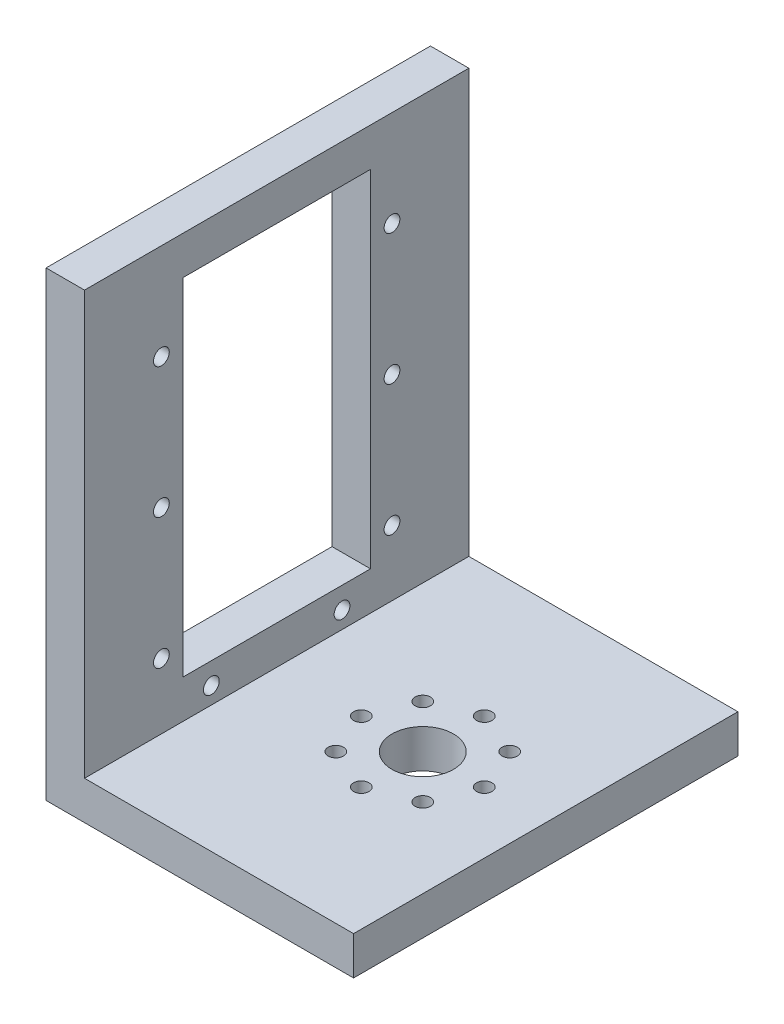
SolidWorks part; units mm, degrees
material "ABS"
ref_plane "Front Plane" through (0, 0, 0) normal (0, 0, 1) x (1, 0, 0)
ref_plane "Top Plane" through (0, 0, 0) normal (0, 1, 0) x (1, 0, 0)
ref_plane "Right Plane" through (0, 0, 0) normal (1, 0, 0) x (0, 0, -1)
sketch "Sketch1" plane through (0, 0, 0) normal (0, 1, 0) x (1, 0, 0)
  line L0 (40, 25) -> (24, 25) construction
  line L1 (0, 0) -> (40, 0)
  line L2 (0, 0) -> (0, 50)
  line L3 (0, 50) -> (40, 50)
  line L4 (40, 0) -> (40, 50)
  line L5 (24, 33) -> (24, 25) construction
  circle A0 centre (24, 25) radius 4
  circle A1 centre (24, 33) radius 1
  circle A2 centre (29.6569, 30.6569) radius 1
  circle A3 centre (32, 25) radius 1
  circle A4 centre (29.6569, 19.3431) radius 1
  circle A5 centre (24, 17) radius 1
  circle A6 centre (18.3431, 19.3431) radius 1
  circle A7 centre (16, 25) radius 1
  circle A8 centre (18.3431, 30.6569) radius 1
  point P26 (24, 25)
  dimension "D3" = 8
  dimension "D5" = 2
  dimension "D1" = 40
  dimension "D2" = 50
  dimension "D4" = 16
  dimension "D7" = 8
  dimension "D6" = 8
extrude "Boss-Extrude1" add sketch "Sketch1" along normal blind 5
sketch "Sketch3" plane through (0, 0, 0) normal (0, 1, 0) x (1, 0, 0)
  line L0 (40, 50) -> (0, 50) construction
  line L1 (0, 0) -> (5, 0)
  line L2 (0, 0) -> (0, 50)
  line L3 (0, 50) -> (5, 50)
  line L4 (5, 0) -> (5, 50)
  dimension "D1" = 5
extrude "Boss-Extrude2" add sketch "Sketch3" along normal blind 60
sketch "Sketch4" plane through (0, 0, 0) normal (-1, 0, 0) x (0, 0, 1)
  line L0 (-25, 60) -> (-25, 23.7384) construction
  line L1 (-50, 60) -> (0, 60) construction
  line L2 (-40, 47.5) -> (-10, 47.5) construction
  line L3 (-37.2, 10) -> (-12.8, 10)
  line L4 (-37.2, 10) -> (-37.2, 55)
  line L5 (-37.2, 55) -> (-12.8, 55)
  line L6 (-12.8, 10) -> (-12.8, 55)
  line L7 (-40, 30.5) -> (-10, 30.5) construction
  line L8 (-40, 13.5) -> (-33.5, 7.2) construction
  line L9 (-40, 30.5) -> (-40, 13.5) construction
  circle A0 centre (-40, 47.5) radius 1.025
  circle A1 centre (-10, 47.5) radius 1.025
  circle A2 centre (-40, 30.5) radius 1.025
  circle A5 centre (-10, 30.5) radius 1.025
  circle A8 centre (-40, 13.5) radius 1.025
  circle A9 centre (-33.5, 7.2) radius 1.025
  circle A10 centre (-16.5, 7.2) radius 1.025
  circle A11 centre (-10, 13.5) radius 1.025
  point P8 (-25, 55)
  point P9 (-25, 55)
  point P12 (-25, 47.5)
  dimension "D4" = 2.05
  dimension "D1" = 24.4
  dimension "D2" = 45
  dimension "D3" = 30
  dimension "D5" = 17
  dimension "D6" = 7.5
  dimension "D7" = 17
  dimension "D8" = 6.5
  dimension "D9" = 6.3
  dimension "D10" = 5
extrude "Cut-Extrude1" cut sketch "Sketch4" against normal through all
